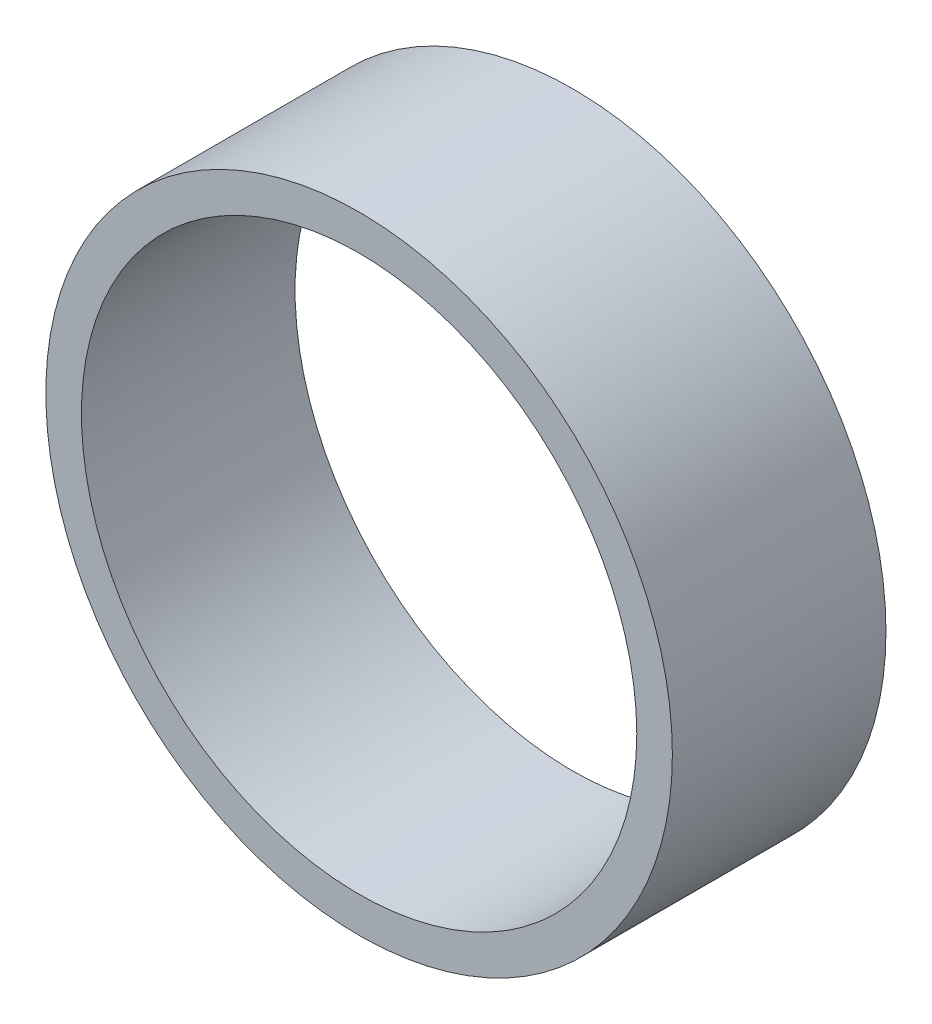
SolidWorks part; units mm, degrees
ref_plane "Plan de face" through (0, 0, 0) normal (0, 0, 1) x (1, 0, 0)
ref_plane "Plan de dessus" through (0, 0, 0) normal (0, 1, 0) x (1, 0, 0)
ref_plane "Plan de droite" through (0, 0, 0) normal (1, 0, 0) x (0, 0, -1)
sketch "Esquisse1" plane through (0, 0, 0) normal (0, 0, 1) x (1, 0, 0)
  circle A0 centre (0, 0) radius 39
  circle A1 centre (0, 0) radius 44
  dimension "D1" = 5
  dimension "D2" = 78
extrude "Boss.-Extru.1" add sketch "Esquisse1" along normal blind 30
